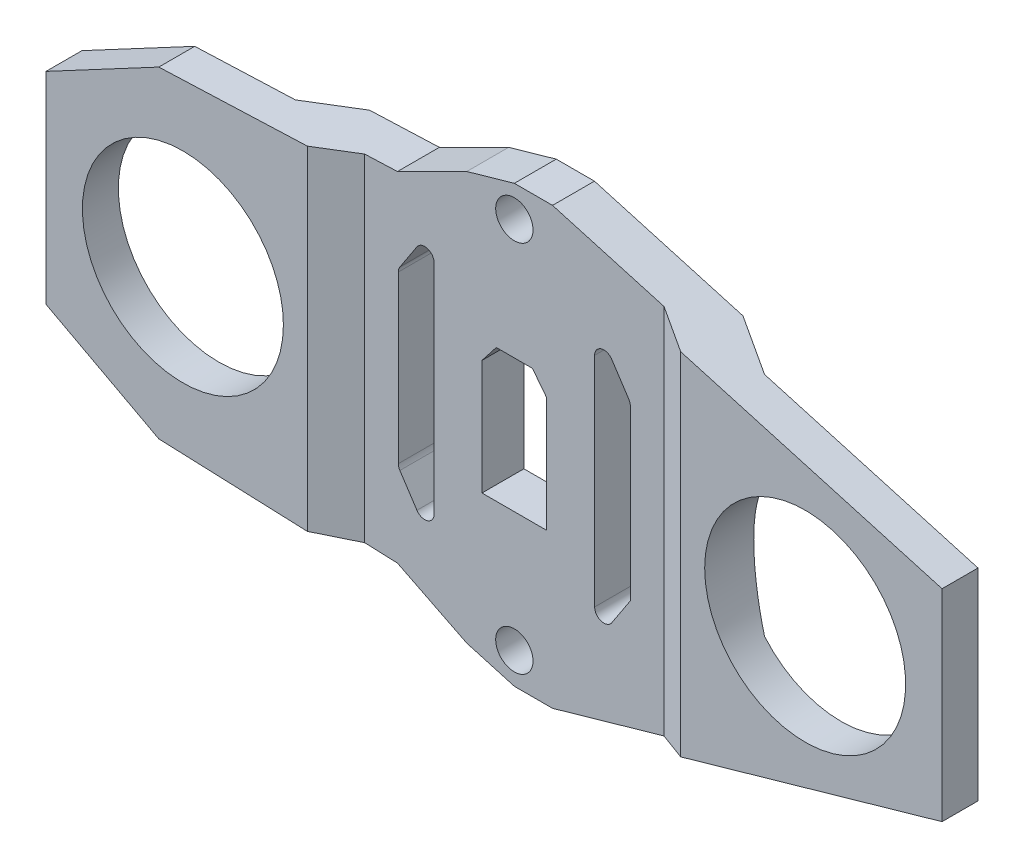
SolidWorks part; units mm, degrees
ref_plane "Front Plane" through (0, 0, 0) normal (0, 0, 1) x (1, 0, 0)
ref_plane "Top Plane" through (0, 0, 0) normal (0, 1, 0) x (1, 0, 0)
ref_plane "Right Plane" through (0, 0, 0) normal (1, 0, 0) x (0, 0, -1)
sketch "Sketch1" plane through (0, 0, 0) normal (0, 0, 1) x (1, 0, 0)
  line L0 (0, 0) -> (-50, 0) construction
  line L1 (0, 0) -> (0, 30) construction
  line L4 (-72, 16.2106) -> (-72, -16.2106)
  line L7 (0, 35) -> (6.1382, 35)
  line L8 (6.1382, 35) -> (72, 16.2106)
  line L9 (72, 16.2106) -> (72, -16.2106)
  line L10 (6.1382, -35) -> (72, -16.2106)
  line L11 (0, 35) -> (-7.6463, 32.8186)
  line L12 (-7.6463, 32.8186) -> (-18.7809, 27.2508)
  line L13 (-18.7809, 27.2508) -> (-53.8745, 25.8731)
  line L14 (-53.8745, 25.8731) -> (-72, 16.2106)
  line L15 (-53.8745, -25.8731) -> (-72, -16.2106)
  line L16 (-18.7809, -27.2508) -> (-53.8745, -25.8731)
  line L17 (-7.6463, -32.8186) -> (-18.7809, -27.2508)
  line L18 (0, -35) -> (-7.6463, -32.8186)
  line L19 (0, -35) -> (6.1382, -35)
  circle A0 centre (0, 30) radius 3
  circle A1 centre (-50, 0) radius 16.15
  circle A2 centre (0, -30) radius 3
  circle A3 centre (50, 0) radius 16.15
  point P7 (-53.8745, 25.8731)
  point P10 (-18.7809, 27.2508)
  point P13 (-72, 0)
  point P22 (0, -35)
  dimension "D1" = 6
  dimension "D3" = 32.3
  dimension "D2" = 50
  dimension "D4" = 30
  dimension "D5" = 72
  dimension "D6" = 70
extrude "Boss-Extrude1" add sketch "Sketch1" along normal blind 10
sketch "Sketch2" plane through (0, 0, 0) normal (0, 1, 0) x (1, 0, 0)
  line L0 (-30, -10) -> (-24.0537, -6.7361)
  line L2 (-24.0537, -6.7361) -> (4.4848, -6.7361)
  line L3 (-30, -10) -> (30, -10)
  line L5 (0, 20.7446) -> (0, -29.3903) construction
  line L6 (-72, 0) -> (-72, -4.2257)
  line L8 (-72, -4.2257) -> (-37.6985, -4.2257)
  line L9 (-37.6985, -4.2257) -> (-30, 0)
  line L10 (-30, 0) -> (-72, 0)
  line L11 (30, 0) -> (72, 0)
  line L12 (37.6985, -4.2257) -> (30, 0)
  line L13 (72, -4.2257) -> (37.6985, -4.2257)
  line L14 (72, 0) -> (72, -4.2257)
  line L15 (24.0537, -6.7361) -> (4.4848, -6.7361)
  line L16 (30, -10) -> (24.0537, -6.7361)
  line L18 (-72, -10) -> (-72, 0) construction
  point P2 (0, 0)
  point P3 (0, 0)
  point P14 (-72, 0)
  point P15 (-72, -4.2257)
  point P16 (0, 0)
  point P19 (-30, 0)
  point P25 (0, -10)
  point P26 (0, 0)
  dimension "D1" = 60
extrude "Cut-Extrude1" cut sketch "Sketch2" against normal through all both and the other way through all
sketch "Sketch3" plane through (0, 0, 6.7361) normal (0, 0, 1) x (1, 0, 0)
  line L0 (5.2, -10.7) -> (-5.2, -10.7)
  line L1 (-5, 10.5) -> (5, 10.5) construction
  line L2 (-5, 10.5) -> (-5, -10.5) construction
  line L3 (-5, -10.5) -> (5, -10.5) construction
  line L4 (5, 10.5) -> (5, -10.5) construction
  line L5 (-5, 10.5) -> (5, -10.5) construction
  line L6 (-5, -10.5) -> (5, 10.5) construction
  line L7 (-5.2, -10.7) -> (-5.2, 7.758)
  line L8 (-5.2, 7.758) -> (-2.9087, 10.7)
  line L9 (-2.9087, 10.7) -> (2.9087, 10.7)
  line L10 (0, 14.3964) -> (0, -14.2533) construction
  line L11 (5.2, -10.7) -> (5.2, 7.758)
  line L12 (5.2, 7.758) -> (2.9087, 10.7)
  point P0 (0, 0)
  point P8 (-5.0058, 7.6497)
  point P15 (0, -10.7)
  point P17 (0, 10.7)
  dimension "D1" = 0.2
  dimension "D2" = 0.2
  dimension "D3" = 0.2
  dimension "D4" = 21
  dimension "D5" = 10
extrude "Cut-Extrude2" cut sketch "Sketch3" against normal through all both and the other way through all
sketch "Sketch4" plane through (0, 0, 6.7361) normal (0, 0, 1) x (1, 0, 0)
  line L0 (-18.6418, 13.7834) -> (-18.6418, -13.7834)
  line L1 (-18.6418, -13.7834) -> (-12.9, -22.5266)
  line L2 (-12.9, -22.5266) -> (-12.9, 22.5266)
  line L3 (-25.9785, 0) -> (17.2443, 0) construction
  line L4 (0, 18.6228) -> (0, -13.7834) construction
  line L5 (-18.6418, 13.7834) -> (-12.9, 22.5266)
  line L6 (18.6418, 13.7834) -> (12.9, 22.5266)
  line L7 (12.9, -22.5266) -> (12.9, 22.5266)
  line L8 (18.6418, -13.7834) -> (12.9, -22.5266)
  line L9 (18.6418, 13.7834) -> (18.6418, -13.7834)
  point P0 (18.6418, 0)
  point P10 (-12.9, 0)
  point P11 (-18.6418, 0)
  point P12 (12.9, 0)
extrude "Cut-Extrude3" cut sketch "Sketch4" against normal through all both and the other way through all
fillet "Fillet1" radius 1.5 7 edges at (18.6418, 13.7834, 3.368) (12.9, 22.5266, 3.368) (12.9, -22.5266, 3.368) (-12.9, -22.5266, 3.368) (-18.6418, -13.7834, 3.368) (-18.6418, 13.7834, 3.368) (-12.9, 22.5266, 3.368)
